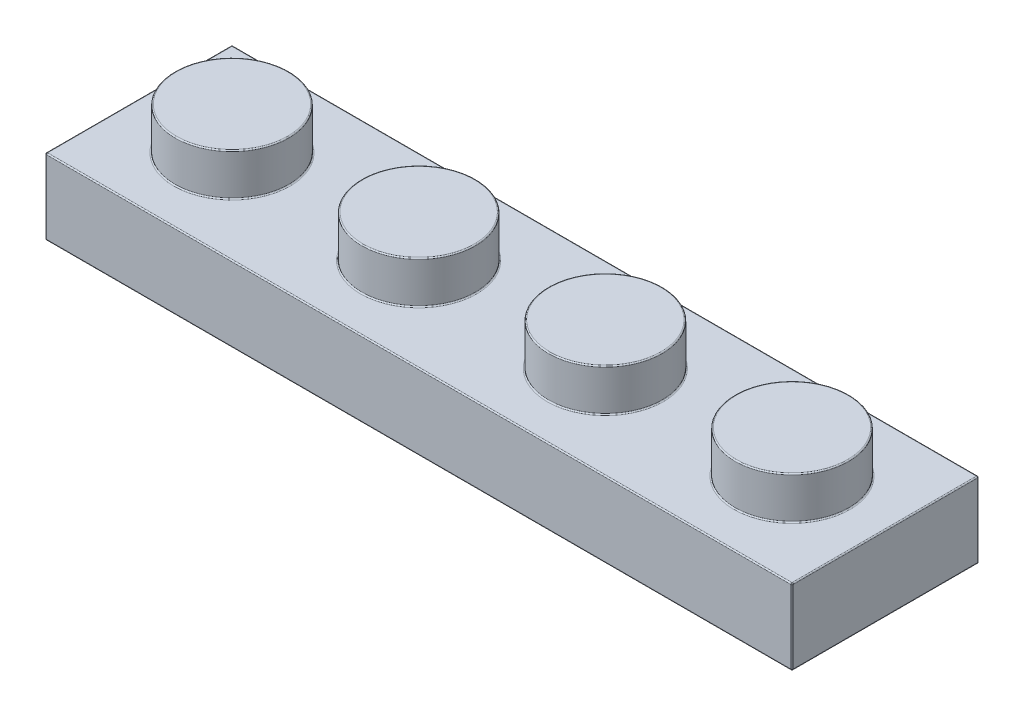
SolidWorks part; units mm, degrees
ref_plane "Front Plane" through (0, 0, 0) normal (0, 0, 1) x (1, 0, 0)
ref_plane "Top Plane" through (0, 0, 0) normal (0, 1, 0) x (1, 0, 0)
ref_plane "Right Plane" through (0, 0, 0) normal (1, 0, 0) x (0, 0, -1)
sketch "Sketch1" plane through (0, 0, 0) normal (0, 1, 0) x (1, 0, 0)
  line L1 (-3.98, 3.98) -> (3.98, 3.98)
  line L2 (-3.98, 3.98) -> (-3.98, -3.98)
  line L3 (-3.98, -3.98) -> (3.98, -3.98)
  line L4 (3.98, 3.98) -> (3.98, -3.98)
  line L5 (-3.98, 3.98) -> (3.98, -3.98) construction
  line L6 (-3.98, -3.98) -> (3.98, 3.98) construction
  point P0 (0, 0)
  dimension "D1" = 7.96
extrude "Extrude1" add sketch "Sketch1" along normal blind 3.22
sketch "Sketch2" plane through (0, 3.22, 0) normal (0, 1, 0) x (1, 0, 0)
  circle A0 centre (0, 0) radius 2.425
  dimension "D1" = 4.85
extrude "Extrude2" add sketch "Sketch2" along normal blind 1.8
pattern_linear "LPattern1" count 4 spacing 7.96 along (1, 0, 0) of "Extrude2", "Extrude1"
shell "Shell1" thickness 1.55
sketch "Sketch3" plane through (0, 1.67, 0) normal (0, -1, 0) x (1, 0, 0)
  line L0 (26.31, 2.43) -> (26.31, -2.43) construction
  line L1 (-2.43, 2.43) -> (26.31, 2.43) construction
  line L2 (-2.43, -2.43) -> (-2.43, 2.43) construction
  line L3 (26.31, -2.43) -> (-2.43, -2.43) construction
  line L4 (26.31, 2.43) -> (26.31, -2.43)
  line L5 (-2.43, 2.43) -> (26.31, 2.43)
  line L6 (-2.43, -2.43) -> (-2.43, 2.43)
  line L7 (26.31, -2.43) -> (-2.43, -2.43)
extrude "Extrude3" cut sketch "Sketch3" against normal blind 0.14
sketch "Sketch5" plane through (0, 1.81, 0) normal (0, -1, 0) x (1, 0, 0)
  line L0 (-2.43, 2.43) -> (26.31, 2.43) construction
  line L1 (0, 2.43) -> (7.96, 2.43) construction
  line L2 (0, 2.43) -> (0, -2.43) construction
  line L3 (0, -2.43) -> (7.96, -2.43) construction
  line L4 (7.96, 2.43) -> (7.96, -2.43) construction
  line L5 (-2.43, -2.43) -> (26.31, -2.43) construction
  line L6 (3.98, 0) -> (11.94, 0) construction
  line L8 (7.96, 2.43) -> (15.92, 2.43) construction
  line L9 (7.96, 2.43) -> (7.96, -2.43) construction
  line L10 (7.96, -2.43) -> (15.92, -2.43) construction
  line L11 (15.92, 2.43) -> (15.92, -2.43) construction
  circle A0 centre (3.98, 0) radius 1.5
  circle A1 centre (3.98, 0) radius 0.64
  circle A2 centre (11.94, 0) radius 1.5
  circle A3 centre (11.94, 0) radius 0.64
  circle A4 centre (19.9, 0) radius 1.5
  circle A5 centre (19.9, 0) radius 0.64
  point P8 (0, 0)
  point P10 (7.96, 0)
  point P15 (3.98, 2.43)
  point P26 (15.92, 0)
  point P28 (11.94, 2.43)
  dimension "D1" = 3
  dimension "D2" = 0.86
  dimension "D3" = 7.96
extrude "Extrude4" add sketch "Sketch5" along normal up to surface (1.81 mm away) up to face at (11.94, 0, 0)
fillet "Fillet1" radius 0.05 52 edges at (19.9, 1.81, -0.64) (19.9, 0, 1.5) (19.9, 0, 0.64) (11.94, 1.81, -0.64) (11.94, 0, 1.5) (11.94, 0, 0.64) (3.98, 1.81, -0.64) (3.98, 0, 1.5) (3.98, 0, 0.64) (11.94, 1.81, 2.43) (-2.43, 1.81, 0) (11.94, 1.81, -2.43) (26.31, 1.81, 0) (23.88, 1.81, 0.875) (15.92, 1.81, 0.875) (7.96, 1.81, 0.875) (0, 1.81, 0.875) (7.96, 3.47, 0.875) (26.31, 0, 0) (26.31, 0.905, 2.43) (26.31, 0.905, -2.43) (0, 3.47, 0.875) (11.94, 0, -2.43) (-2.43, 0, 0) (11.94, 0, 2.43) (-2.43, 0.905, 2.43) (-2.43, 0.905, -2.43) (15.92, 3.47, 0.875) (23.88, 3.47, 0.875) (7.96, 3.22, 2.425) (7.96, 5.02, 2.425) (27.86, 0, 0) (27.86, 3.22, 0) (27.86, 1.61, -3.98) (27.86, 1.61, 3.98) (0, 3.22, 2.425) (0, 5.02, 2.425) (11.94, 0, -3.98) (-3.98, 0, 0) (11.94, 0, 3.98) (11.94, 3.22, -3.98) (-3.98, 3.22, 0) (11.94, 3.22, 3.98) (-3.98, 1.61, 3.98) (-3.98, 1.61, -3.98) (15.92, 3.22, 2.425) (15.92, 5.02, 2.425) (23.88, 3.22, 2.425) (23.88, 5.02, 2.425) (3.98, 1.81, 1.5) (11.94, 1.81, 1.5) (19.9, 1.81, 1.5)
